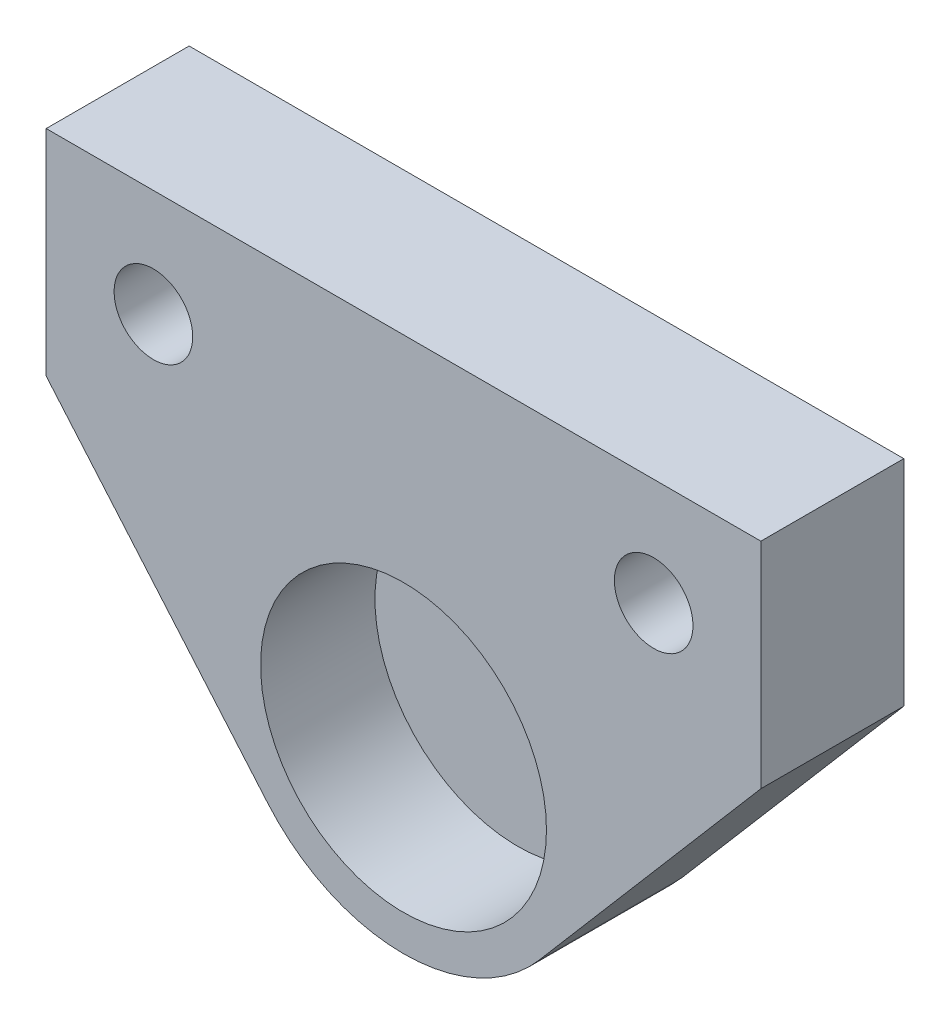
SolidWorks part; units mm, degrees
material "PA Typ 6"
ref_plane "Vorne" through (0, 0, 0) normal (0, 0, 1) x (1, 0, 0)
ref_plane "Oben" through (0, 0, 0) normal (0, 1, 0) x (1, 0, 0)
ref_plane "Rechts" through (0, 0, 0) normal (1, 0, 0) x (0, 0, -1)
sketch "Skizze1" plane through (0, 0, 0) normal (0, 0, 1) x (1, 0, 0)
  line L0 (-9.4997, -8.1243) -> (-25, 10)
  line L1 (-25, 10) -> (-25, 25)
  line L2 (-25, 25) -> (25, 25)
  line L3 (25, 25) -> (25, 10)
  line L4 (25, 10) -> (9.4997, -8.1243)
  line L5 (0, 0) -> (0, 25) construction
  arc A0 (-9.4997, -8.1243) -> (9.4997, -8.1243) centre (0, 0) ccw
  dimension "D1" = 25
  dimension "D2" = 25
  dimension "D3" = 15
  dimension "D4" = 50
extrude "Aufsatz-Linear austragen1" add sketch "Skizze1" along normal blind 10
sketch "Skizze2" plane through (0, 0, 10) normal (0, 0, 1) x (1, 0, 0)
  circle A0 centre (0, 0) radius 10
extrude "Schnitt-Linear austragen1" cut sketch "Skizze2" against normal blind 8
hole_wizard "Formsenkung für M5 Senkschraube mit Innensechskant1" positions "Skizze3" profile "Skizze4" countersink size "M5" standard "DIN" end condition up to next
sketch "Skizze3" plane through (0, 0, 0) normal (0, 0, -1) x (-1, 0, 0)
  line L0 (-17.5, 17.4991) -> (17.5, 17.4991) construction
  line L3 (-25, 25) -> (25, 25) construction
  point P0 (-17.5, 17.4991)
  point P2 (17.5, 17.4991)
  point P14 (0, 17.4991)
  dimension "D1" = 7.5009
  dimension "D2" = 35
sketch "Skizze4" plane through (17.5, 17.4991, 0) normal (1, 0, 0) x (0, 1, 0)
  line L0 (0, 0) -> (0, 10)
  line L1 (0, 10) -> (2.75, 10)
  line L2 (2.75, 10) -> (2.75, 2.985)
  line L3 (2.75, 2.985) -> (5.735, 0)
  line L5 (5.735, 0) -> (0, 0)
  line L6 (-2.75, 2.985) -> (-5.735, 0) construction
  line L11 (0, -6.35) -> (0, 107.95) construction
  dimension "Bohrerdurchmesser" = 5.5
  dimension "Bohrungstiefe" = 10
  dimension "Senkdurchmesser (Oben)" = 11.47
  dimension "Senkwinkel (Oben)" = 90
